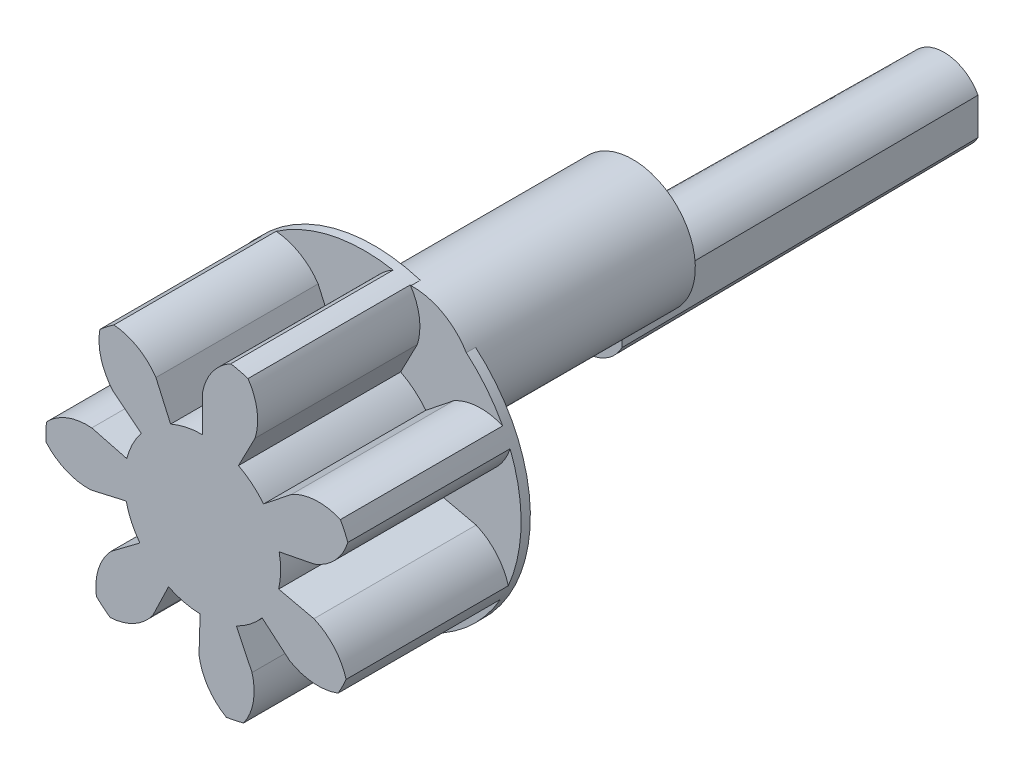
SolidWorks part; units mm, degrees
ref_plane "Front Plane" through (0, 0, 0) normal (0, 0, 1) x (1, 0, 0)
ref_plane "Top Plane" through (0, 0, 0) normal (0, 1, 0) x (1, 0, 0)
ref_plane "Right Plane" through (0, 0, 0) normal (1, 0, 0) x (0, 0, -1)
sketch "Sketch2" plane through (0, 0, 0) normal (0, 0, 1) x (1, 0, 0)
  circle A0 centre (0, 0) radius 6.75
  dimension "D1" = 13.5
extrude "gear outside diameter" add sketch "Sketch2" along normal blind 7
sketch "Sketch1" plane through (0, 0, 0) normal (0, 0, 1) x (1, 0, 0)
  line L0 (0, 4.9334) -> (0, 0) construction
  line L1 (0, 0) -> (0.0782, 5.2494) construction
  line L2 (0, 0) -> (1.226, 6.6377) construction
  line L3 (0, 0) -> (-3.239, 15.2342) construction
  line L4 (0, 4.9334) -> (0, 3.375)
  line L5 (-2.0071, 4.5066) -> (-1.3731, 3.0831)
  circle A0 centre (0, 0) radius 6.75 construction
  circle A1 centre (0, 0) radius 5.25 construction
  circle A2 centre (0, 0) radius 4.9334 construction
  arc A3 (1.226, 6.6377) -> (0, 4.9334) centre (2.3857, 4.5104) ccw
  arc A4 (-3.8204, 5.5648) -> (-2.0071, 4.5066) centre (-4.0143, 3.1497) cw
  arc A5 (-3.8204, 5.5648) -> (1.226, 6.6377) centre (0, 0) cw
  arc A6 (0, 3.375) -> (-1.3731, 3.0831) centre (0, 0) ccw
  dimension "D1" = 13.5
  dimension "D2" = 10.5
  dimension "D3" = 9.8668
  dimension "D7" = 6.75
  dimension "D4" = 12.857
  dimension "D5" = 0.854
  dimension "D6" = 10.464
extrude "gear tooth cut" cut sketch "Sketch1" along normal through all
pattern_circular "gear teeth" count 7 over 360 about axis through (0, 0, 0) along (0, 0, 1) of "gear tooth cut"
sketch "Sketch3" plane through (0, 0, 0) normal (0, 0, 1) x (1, 0, 0)
  circle A0 centre (0, 0) radius 3.375
  dimension "D1" = 6.75
extrude "gear dedendum circle" add sketch "Sketch3" along normal up to surface (7 mm away) up to face at (0, 0, 7)
sketch "Sketch5" plane through (0, 0, 0) normal (0, 0, -1) x (-1, 0, 0)
  circle A0 centre (0, 0) radius 8
  dimension "D1" = 16
extrude "Boss-Extrude1" [suppressed] add sketch "Sketch5" along normal blind 1
sketch "Sketch4" plane through (0, 0, 7) normal (0, 0, 1) x (1, 0, 0)
  line L0 (-1.1832, -1.15) -> (1.1832, -1.15)
  arc A0 (1.1832, -1.15) -> (-1.1832, -1.15) centre (0, 0) ccw
  point P5 (0, 1.65)
  dimension "D1" = 3.3
  dimension "D2" = 2.8
extrude "Cut-Extrude1" [suppressed] cut sketch "Sketch4" against normal through all
chamfer "Chamfer1" [suppressed] distance 1.5 angle 45
chamfer "Chamfer2" [suppressed] distance 0.5 angle 45
sketch "Sketch8" plane through (0, 0, 0) normal (0, 0, -1) x (-1, 0, 0)
  circle A0 centre (-2.068, 3.7469) radius 2.7
  circle A1 centre (-2.068, 3.7469) radius 3 construction
  circle A2 centre (-2.068, 3.7469) radius 3 construction
  dimension "D1" = 0.3
extrude "Boss-Extrude3" add sketch "Sketch8" along normal blind 9.5
sketch "Sketch6" plane through (0, 0, -9.5) normal (0, 0, -1) x (-1, 0, 0)
  line L0 (1.6, 0.8246) -> (1.6, 0.6)
  line L1 (-1.6, 0.8246) -> (-1.6, -0.8246)
  line L2 (1.6, 0) -> (-1.6, 0) construction
  line L3 (1.6971, 0.6) -> (1.6971, -0.6)
  line L4 (1.6971, 0.6) -> (1.6, 0.6)
  line L5 (1.6971, -0.6) -> (1.6, -0.6)
  line L6 (1.6, -0.6) -> (1.6, -0.8246)
  line L7 (1.6, 0) -> (1.6971, 0) construction
  arc A0 (-1.6, -0.8246) -> (1.6, -0.8246) centre (0, 0) ccw
  arc A1 (1.6, 0.8246) -> (-1.6, 0.8246) centre (0, 0) ccw
  dimension "D1" = 3.6
  dimension "D2" = 3.2
  dimension "D3" = 1.2
extrude "Boss-Extrude2" add sketch "Sketch6" along normal blind 15.5 draft 0.5
sketch "Sketch9" plane through (0, 0, 0) normal (0, 0, -1) x (-1, 0, 0)
  circle A0 centre (0, 0) radius 6.75
  arc A1 (6.7441, -0.2818) -> (6.7327, 0.4827) centre (0, 0) ccw construction
extrude "Boss-Extrude4" add sketch "Sketch9" along normal blind 0.4
sketch "Sketch7" plane through (0, 0, 15) normal (0, 0, 1) x (1, 0, 0)
  circle A0 centre (0, 0) radius 0.7141
equation "\"N\" = 7'Number of teeth"
equation "\"m\"= 1.5'module  (using 25.4/P for imperial gears)"
equation "\"F\" = 7'face width"
equation "\"phi\"=20 'pressure angle"
equation "\"d\"=\"N\"*\"m\""
equation "\"OD\"=(\"N\"+2)*\"m\""
equation "\"db\"=\"d\"* cos( \"phi\" ) "
equation "\"D5@Sketch1\"= (tan( \"phi\" )-\"phi\" * pi /180)*180/ pi "
equation "\"D2@Sketch1\" = \"d\""
equation "\"D3@Sketch1\"=\"db\""
equation "\"D1@Sketch1\"=\"OD\""
equation "\"phiB\"= arccos( \"db\"/\"OD\" ) "
equation "\"D6@Sketch1\"=tan(\"phiB\")*180 /  pi -\"phiB\""
equation "\"D4@Sketch1\" = 360/\"N\"/4"
equation "\"D1@Sketch2\" = \"OD\""
equation "\"D1@gear teeth\"=\"N\""
equation "\"x\"=2.5-\"N\"*(1-cos(\"phi\"))"
equation "\"D1@Sketch3\" = (\"N\"-2.5)*\"m\""
equation "\"D7@Sketch1\" = (\"N\"-2.5)*\"m\""
equation "\"D1@gear outside diameter\" = \"F\""
